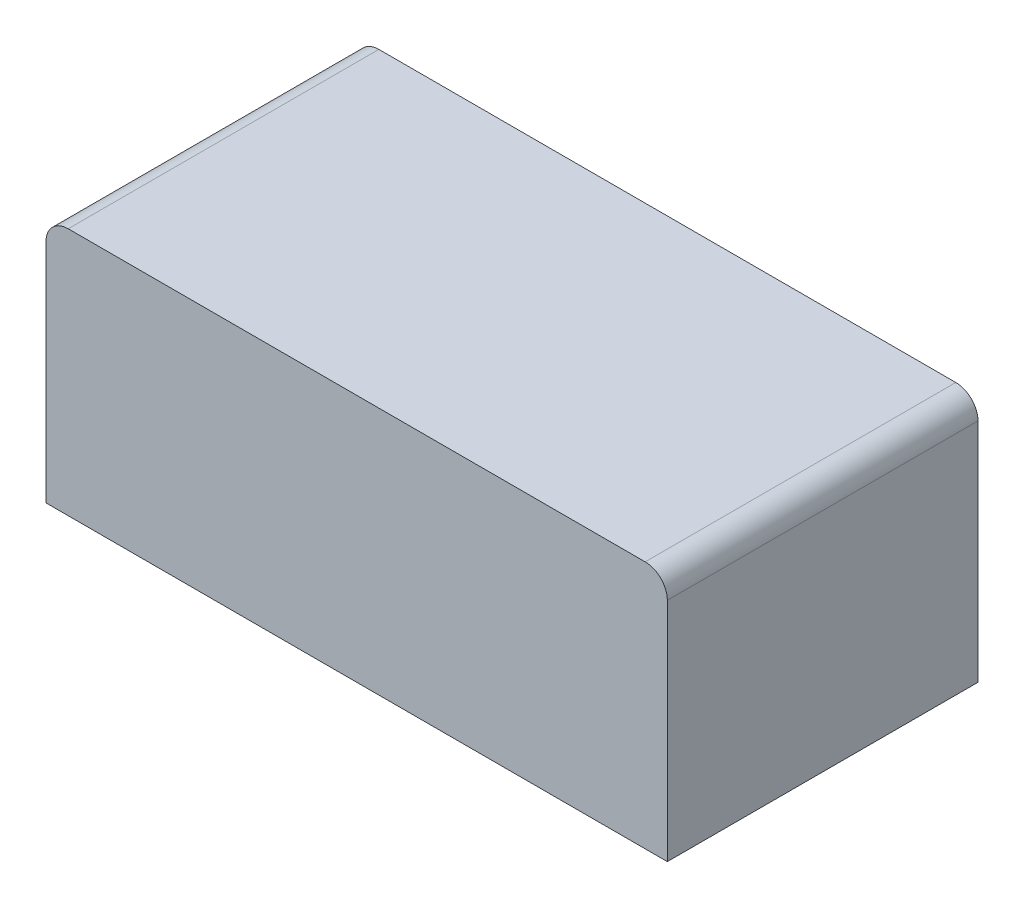
SolidWorks part; units mm, degrees
ref_plane "Front Plane" through (0, 0, 0) normal (0, 0, 1) x (1, 0, 0)
ref_plane "Top Plane" through (0, 0, 0) normal (0, 1, 0) x (1, 0, 0)
ref_plane "Right Plane" through (0, 0, 0) normal (1, 0, 0) x (0, 0, -1)
sketch "Sketch1" plane through (0, 0, 0) normal (0, 1, 0) x (1, 0, 0)
  line L0 (1.4, -0.7) -> (1.4, 0.7)
  line L1 (1.4, -0.7) -> (-1.4, -0.7)
  line L2 (1.4, 0.7) -> (-1.4, 0.7)
  line L3 (-1.4, -0.7) -> (-1.4, 0.7)
  line L4 (1.4, -0.7) -> (-1.4, 0.7) construction
  line L5 (1.4, 0.7) -> (-1.4, -0.7) construction
  point P1 (0, 0)
  dimension "D1" = 2.8
  dimension "D2" = 1.4
extrude "Boss-Extrude1" add sketch "Sketch1" along normal blind 1.12
fillet "Fillet1" radius 0.1 2 edges at (1.4, 1.12, 0) (-1.4, 1.12, 0)
